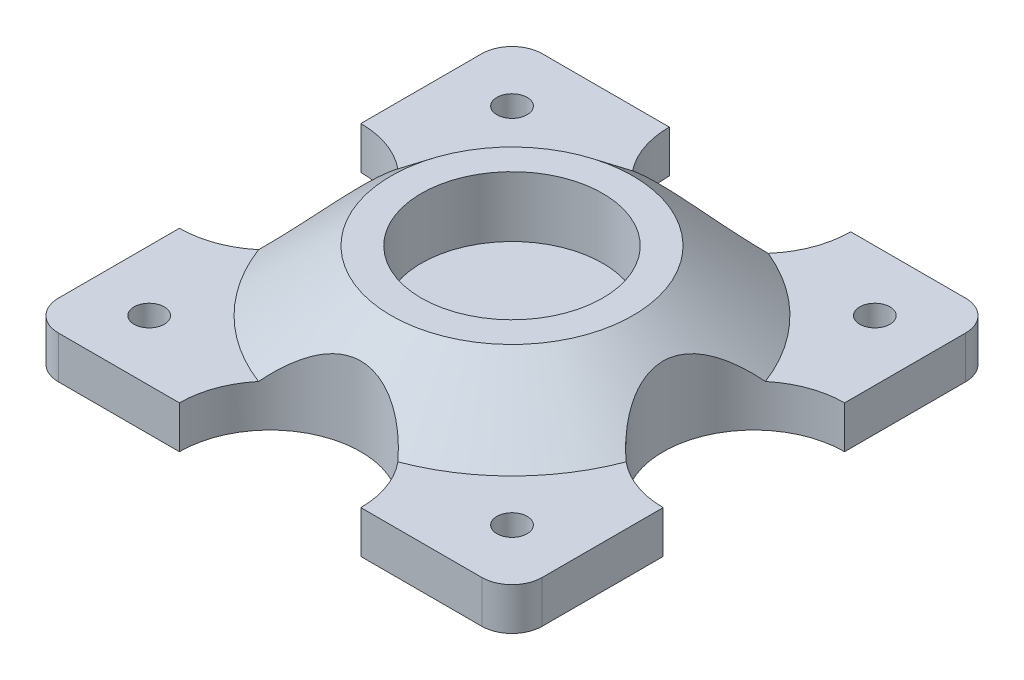
SolidWorks part; units mm, degrees
ref_plane "Front Plane" through (0, 0, 0) normal (0, 0, 1) x (1, 0, 0)
ref_plane "Top Plane" through (0, 0, 0) normal (0, 1, 0) x (1, 0, 0)
ref_plane "Right Plane" through (0, 0, 0) normal (1, 0, 0) x (0, 0, -1)
sketch "Sketch1" plane through (0, 0, 0) normal (0, 1, 0) x (1, 0, 0)
  line L6 (-44.45, -50.8) -> (44.45, -50.8)
  line L10 (-50.8, -44.45) -> (-50.8, 44.45)
  line L11 (-44.45, 50.8) -> (44.45, 50.8)
  line L12 (50.8, -44.45) -> (50.8, 44.45)
  line L13 (-50.8, -50.8) -> (50.8, 50.8) construction
  line L14 (-50.8, 50.8) -> (50.8, -50.8) construction
  arc A12 (-50.8, -44.45) -> (-44.45, -50.8) centre (-44.45, -44.45) ccw
  arc A13 (44.45, -50.8) -> (50.8, -44.45) centre (44.45, -44.45) ccw
  arc A14 (50.8, 44.45) -> (44.45, 50.8) centre (44.45, 44.45) ccw
  arc A15 (-44.45, 50.8) -> (-50.8, 44.45) centre (-44.45, 44.45) ccw
  point P0 (0, 0)
  dimension "D3" = 6.35
  dimension "D1" = 101.6
  dimension "D2" = 101.6
extrude "Boss-Extrude2" add sketch "Sketch1" along normal blind 8.89
sketch "Sketch10" plane through (0, 0, 0) normal (0, 0, 1) x (1, 0, 0)
  line L0 (0, 0) -> (0, 45.7203) construction
  line L1 (0, 21.59) -> (0, 8.89)
  line L4 (0, 21.59) -> (25.4, 21.59)
  line L8 (0, 8.89) -> (41.275, 8.89)
  line L11 (25.4, 21.59) -> (41.275, 8.89)
  point P3 (41.275, 0)
  point P4 (41.275, 45.7203)
  point P5 (-44.45, 0)
  point P6 (44.45, 0)
  point P7 (-44.45, 21.59)
  point P8 (44.45, 21.59)
  point P9 (25.4, 0)
  point P10 (25.4, 45.7203)
  point P13 (0, 0)
  point P14 (0, 0)
revolve "Revolve1" add sketch "Sketch10" angle 360 about L0
sketch "Sketch11" plane through (0, 21.59, 0) normal (0, 1, 0) x (1, 0, 0)
  line L6 (50.8, -44.45) -> (50.8, 44.45) construction
  circle A0 centre (1.2815, 50.8) radius 19.05
  circle A1 centre (50.8, 0) radius 19.05
  circle A2 centre (0, -50.8) radius 19.05
  circle A3 centre (-50.8, 0) radius 19.05
  dimension "D1" = 38.1
  dimension "D2" = 38.1
  dimension "D3" = 38.1
  dimension "D4" = 38.1
extrude "Cut-Extrude1" cut sketch "Sketch11" against normal blind 127
sketch "Sketch12" plane through (0, 21.59, 0) normal (0, 1, 0) x (1, 0, 0)
  circle A0 centre (0, 0) radius 19.05
  dimension "D1" = 38.1
extrude "Cut-Extrude2" cut sketch "Sketch12" against normal blind 12.7
sketch "Sketch13" plane through (0, 8.89, 0) normal (0, 1, 0) x (1, 0, 0)
  line L0 (0, 50.6937) -> (0, -52.3581) construction
  line L1 (-57.8389, 0) -> (57.5661, 0) construction
  circle A0 centre (-38.1, 38.1) radius 3.175
  circle A1 centre (38.1, 38.1) radius 3.175
  circle A2 centre (38.1, -38.1) radius 3.175
  circle A3 centre (-38.1, -38.1) radius 3.175
  dimension "D1" = 6.35
  dimension "D2" = 38.1
  dimension "D3" = 38.1
extrude "Cut-Extrude3" cut sketch "Sketch13" against normal blind 12.7
